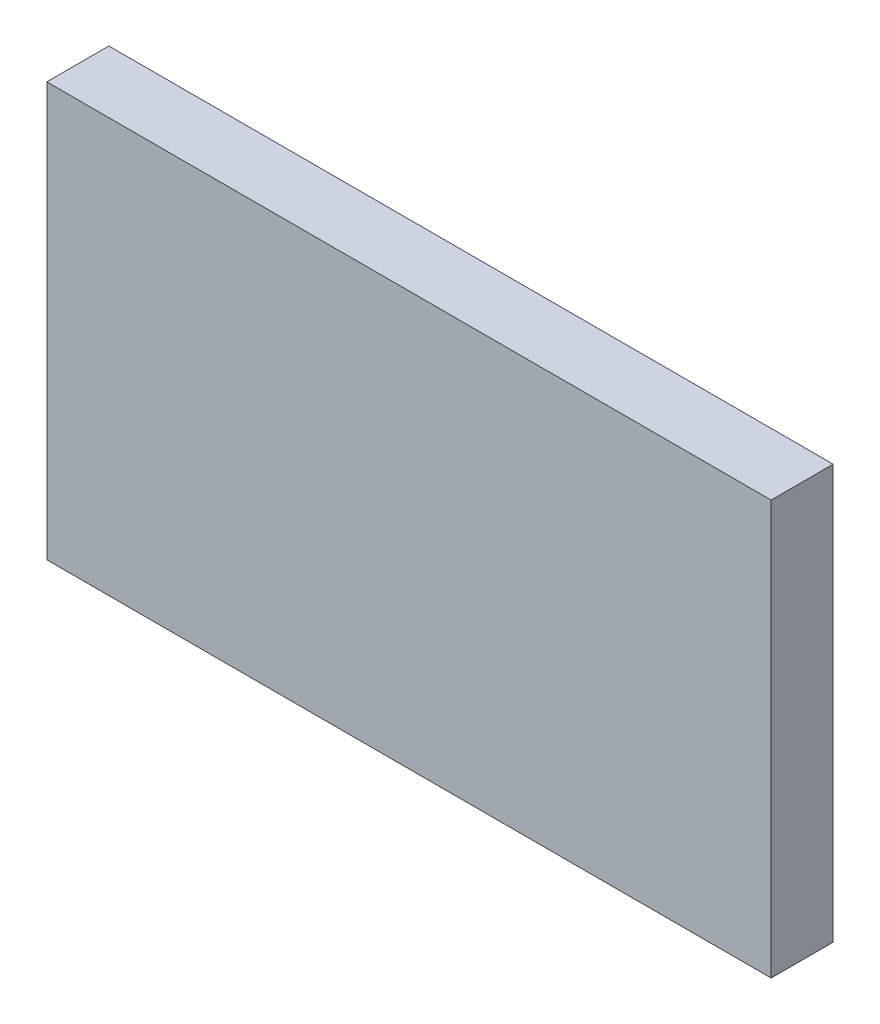
SolidWorks part; units mm, degrees
ref_plane "Plan de face" through (0, 0, 0) normal (0, 0, 1) x (1, 0, 0)
ref_plane "Plan de dessus" through (0, 0, 0) normal (0, 1, 0) x (1, 0, 0)
ref_plane "Plan de droite" through (0, 0, 0) normal (1, 0, 0) x (0, 0, -1)
sketch "Esquisse1" plane through (0, 0, 0) normal (0, 0, 1) x (1, 0, 0)
  line L1 (-17.9136, 11.14) -> (17.0864, 11.14)
  line L2 (-17.9136, 11.14) -> (-17.9136, -8.86)
  line L3 (-17.9136, -8.86) -> (17.0864, -8.86)
  line L4 (17.0864, 11.14) -> (17.0864, -8.86)
  dimension "D1" = 20
  dimension "D2" = 35
extrude "Boss.-Extru.1" add sketch "Esquisse1" along normal blind 3
sketch "Esquisse2" plane through (0, 0, 3) normal (0, 0, 1) x (1, 0, 0)
  line L0 (-4.5708, 0) -> (-36.2035, 0) construction
  line L1 (-36.2035, 0) -> (32.7647, 0) construction
